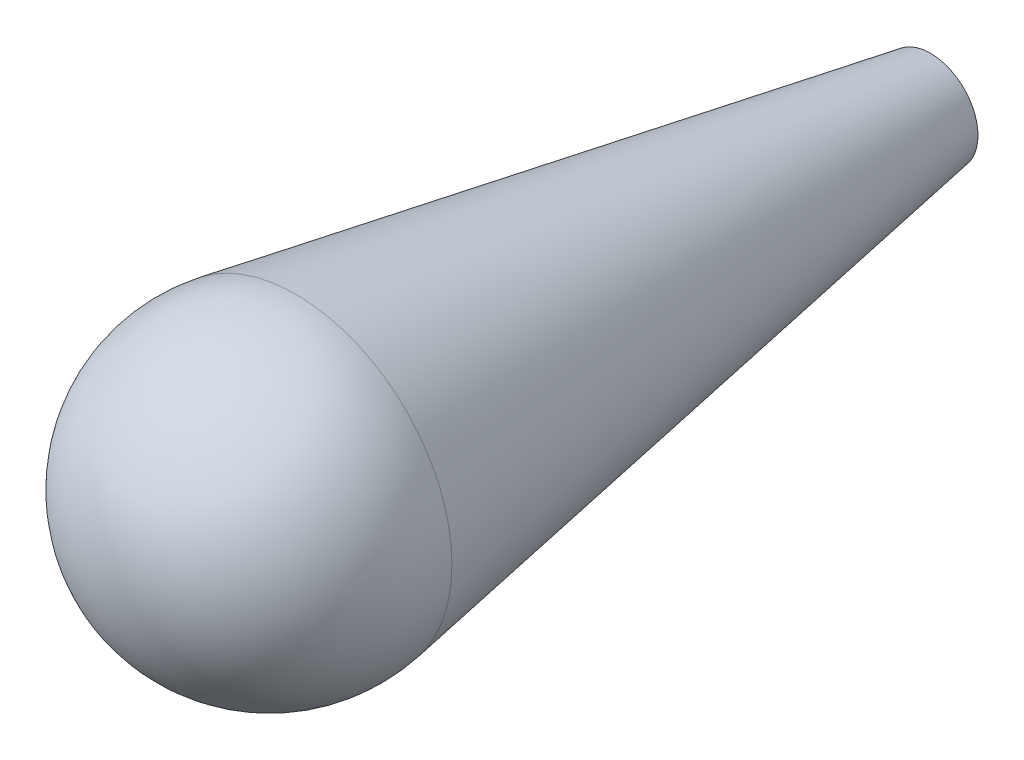
SolidWorks part; units mm, degrees
material "硅橡胶"
ref_plane "前视基准面" through (0, 0, 0) normal (0, 0, 1) x (1, 0, 0)
ref_plane "上视基准面" through (0, 0, 0) normal (0, 1, 0) x (1, 0, 0)
ref_plane "右视基准面" through (0, 0, 0) normal (1, 0, 0) x (0, 0, -1)
sketch "草图1" plane through (0, 0, 0) normal (0, 0, 1) x (1, 0, 0)
  line L0 (4.1432, -9.1013) -> (-4.1432, 9.1013)
  arc A0 (-4.1432, 9.1013) -> (4.1432, -9.1013) centre (0, 0) ccw
revolve "旋转1" add sketch "草图1" angle 360 about L0
sketch "草图2" plane through (0, 0, 0) normal (0, 0, 1) x (1, 0, 0)
  circle A0 centre (0, 0) radius 3
extrude "切除-拉伸1" cut sketch "草图2" against normal through all
sketch "草图3" plane through (0, 0, 0) normal (0, 0, -1) x (-1, 0, 0)
  circle A0 centre (0, 0) radius 3
extrude "凸台-拉伸1" add sketch "草图3" along normal blind 40
sketch "草图4" plane through (0, 0, 0) normal (0, 1, 0) x (1, 0, 0)
  line L0 (-3, 0.5127) -> (-9.8571, 1.6846)
  line L1 (-9.8571, 1.6846) -> (-3, 41.8083)
  line L2 (-3, 40) -> (-3, 46.6456) construction
  line L3 (-3, 41.8083) -> (-3, 0.5127)
  line L4 (0, 0) -> (0, 36.2564) construction
  arc A0 (-3, 9.5394) -> (3, 9.5394) centre (0, 0) ccw construction
revolve "旋转2" add sketch "草图4" angle 360 about L4
sketch "草图5" plane through (0, 0, -40) normal (0, 0, -1) x (-1, 0, 0)
  circle A0 centre (0, 0) radius 3
extrude "切除-拉伸2" cut sketch "草图5" along direction (0, 0, 1) on the side against the normal up to surface (40 mm away) up to plane "前视基准面"
